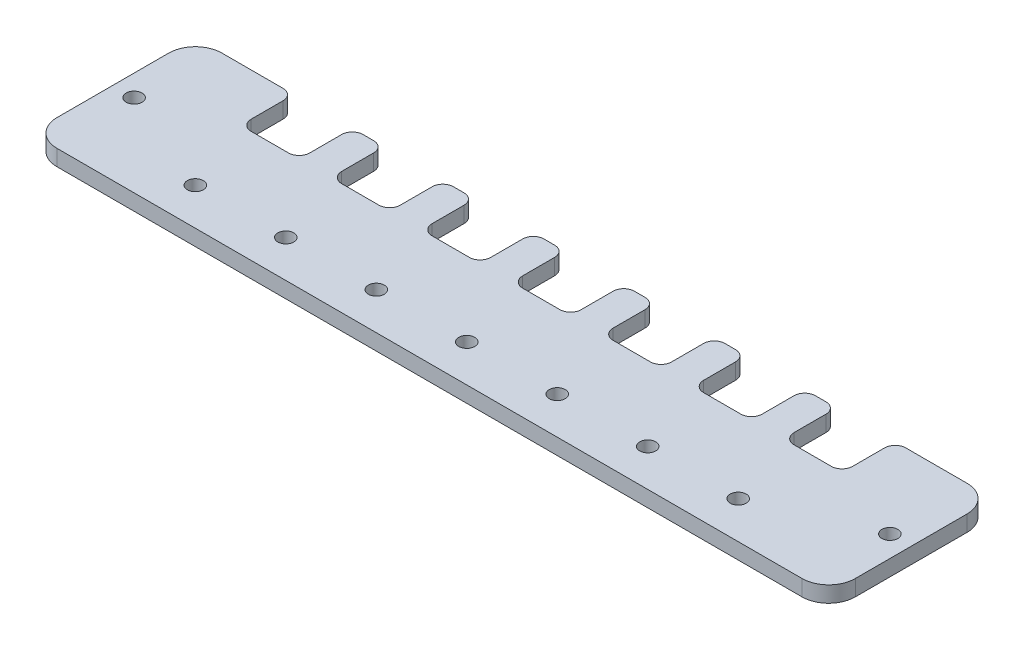
SolidWorks part; units mm, degrees
ref_plane "Front Plane" through (0, 0, 0) normal (0, 0, 1) x (1, 0, 0)
ref_plane "Top Plane" through (0, 0, 0) normal (0, 1, 0) x (1, 0, 0)
ref_plane "Right Plane" through (0, 0, 0) normal (1, 0, 0) x (0, 0, -1)
sketch "Sketch1" plane through (0, 0, 0) normal (0, 1, 0) x (1, 0, 0)
  line L0 (-75, -8.5) -> (75, -8.5) construction
  line L1 (70, 15.5) -> (58.5, 15.5)
  line L2 (75, 10.5) -> (75, -10.5)
  line L3 (70, -15.5) -> (-70, -15.5)
  line L4 (-75, 10.5) -> (-75, -10.5)
  line L5 (75, 15.5) -> (-75, -15.5) construction
  line L6 (75, -15.5) -> (-75, 15.5) construction
  line L7 (-75, 0) -> (75, 0) construction
  line L8 (0, 17.5) -> (0, -15.5) construction
  line L9 (-56.5, 7.5) -> (56.5, 7.5) construction
  line L10 (-54.5, 7.5) -> (-47.5, 7.5) construction
  line L12 (-54.5, 5.5) -> (-47.5, 5.5)
  line L15 (-58.5, 15.5) -> (-70, 15.5)
  line L18 (-51, -8.5) -> (-51, 7.5) construction
  line L21 (-37.5, 5.5) -> (-30.5, 5.5)
  line L24 (-39.5, 7.5) -> (-39.5, 13.5)
  line L27 (-28.5, 7.5) -> (-28.5, 13.5)
  line L30 (-37.5, 7.5) -> (-30.5, 7.5) construction
  line L31 (-20.5, 5.5) -> (-13.5, 5.5)
  line L32 (-56.5, 7.5) -> (-56.5, 13.5)
  line L33 (-45.5, 7.5) -> (-45.5, 13.5)
  line L34 (-22.5, 7.5) -> (-22.5, 13.5)
  line L35 (-11.5, 7.5) -> (-11.5, 13.5)
  line L36 (-20.5, 7.5) -> (-13.5, 7.5) construction
  line L37 (-3.5, 5.5) -> (3.5, 5.5)
  line L38 (-5.5, 7.5) -> (-5.5, 13.5)
  line L39 (5.5, 7.5) -> (5.5, 13.5)
  line L40 (-3.5, 7.5) -> (3.5, 7.5) construction
  line L41 (13.5, 5.5) -> (20.5, 5.5)
  line L42 (11.5, 7.5) -> (11.5, 13.5)
  line L43 (22.5, 7.5) -> (22.5, 13.5)
  line L44 (13.5, 7.5) -> (20.5, 7.5) construction
  line L45 (30.5, 5.5) -> (37.5, 5.5)
  line L46 (28.5, 7.5) -> (28.5, 13.5)
  line L47 (39.5, 7.5) -> (39.5, 13.5)
  line L48 (30.5, 7.5) -> (37.5, 7.5) construction
  line L49 (47.5, 5.5) -> (54.5, 5.5)
  line L50 (45.5, 7.5) -> (45.5, 13.5)
  line L51 (56.5, 7.5) -> (56.5, 13.5)
  line L52 (47.5, 7.5) -> (54.5, 7.5) construction
  line L53 (-41.5, 15.5) -> (-43.5, 15.5)
  line L54 (-24.5, 15.5) -> (-26.5, 15.5)
  line L55 (-7.5, 15.5) -> (-9.5, 15.5)
  line L56 (9.5, 15.5) -> (7.5, 15.5)
  line L57 (26.5, 15.5) -> (24.5, 15.5)
  line L58 (43.5, 15.5) -> (41.5, 15.5)
  circle A1 centre (71, 0) radius 1.5
  arc A2 (-56.5, 7.5) -> (-54.5, 5.5) centre (-54.5, 7.5) ccw
  arc A3 (-47.5, 5.5) -> (-45.5, 7.5) centre (-47.5, 7.5) ccw
  circle A16 centre (-51, -8.5) radius 1.5
  circle A17 centre (-34, -8.5) radius 1.5
  circle A18 centre (-17, -8.5) radius 1.5
  circle A19 centre (0, -8.5) radius 1.5
  circle A20 centre (17, -8.5) radius 1.5
  circle A21 centre (34, -8.5) radius 1.5
  circle A22 centre (51, -8.5) radius 1.5
  arc A23 (70, 15.5) -> (75, 10.5) centre (70, 10.5) cw
  arc A24 (75, -10.5) -> (70, -15.5) centre (70, -10.5) cw
  arc A25 (-70, -15.5) -> (-75, -10.5) centre (-70, -10.5) cw
  arc A26 (-70, 15.5) -> (-75, 10.5) centre (-70, 10.5) ccw
  arc A27 (-45.5, 13.5) -> (-43.5, 15.5) centre (-43.5, 13.5) cw
  arc A28 (-56.5, 13.5) -> (-58.5, 15.5) centre (-58.5, 13.5) ccw
  arc A29 (-39.5, 7.5) -> (-37.5, 5.5) centre (-37.5, 7.5) ccw
  arc A30 (-30.5, 5.5) -> (-28.5, 7.5) centre (-30.5, 7.5) ccw
  arc A31 (-28.5, 13.5) -> (-26.5, 15.5) centre (-26.5, 13.5) cw
  arc A32 (-39.5, 13.5) -> (-41.5, 15.5) centre (-41.5, 13.5) ccw
  arc A33 (-22.5, 7.5) -> (-20.5, 5.5) centre (-20.5, 7.5) ccw
  arc A34 (-13.5, 5.5) -> (-11.5, 7.5) centre (-13.5, 7.5) ccw
  arc A35 (-11.5, 13.5) -> (-9.5, 15.5) centre (-9.5, 13.5) cw
  arc A36 (-22.5, 13.5) -> (-24.5, 15.5) centre (-24.5, 13.5) ccw
  arc A37 (-5.5, 7.5) -> (-3.5, 5.5) centre (-3.5, 7.5) ccw
  arc A38 (3.5, 5.5) -> (5.5, 7.5) centre (3.5, 7.5) ccw
  arc A39 (5.5, 13.5) -> (7.5, 15.5) centre (7.5, 13.5) cw
  arc A40 (-5.5, 13.5) -> (-7.5, 15.5) centre (-7.5, 13.5) ccw
  arc A41 (11.5, 7.5) -> (13.5, 5.5) centre (13.5, 7.5) ccw
  arc A42 (20.5, 5.5) -> (22.5, 7.5) centre (20.5, 7.5) ccw
  arc A43 (22.5, 13.5) -> (24.5, 15.5) centre (24.5, 13.5) cw
  arc A44 (11.5, 13.5) -> (9.5, 15.5) centre (9.5, 13.5) ccw
  arc A45 (28.5, 7.5) -> (30.5, 5.5) centre (30.5, 7.5) ccw
  arc A46 (37.5, 5.5) -> (39.5, 7.5) centre (37.5, 7.5) ccw
  arc A47 (39.5, 13.5) -> (41.5, 15.5) centre (41.5, 13.5) cw
  arc A48 (28.5, 13.5) -> (26.5, 15.5) centre (26.5, 13.5) ccw
  arc A49 (45.5, 7.5) -> (47.5, 5.5) centre (47.5, 7.5) ccw
  arc A50 (54.5, 5.5) -> (56.5, 7.5) centre (54.5, 7.5) ccw
  arc A51 (56.5, 13.5) -> (58.5, 15.5) centre (58.5, 13.5) cw
  arc A52 (45.5, 13.5) -> (43.5, 15.5) centre (43.5, 13.5) ccw
  circle A53 centre (-71, 0) radius 1.5
  point P0 (0, 0)
  point P29 (-56.5, 15.5)
  point P31 (0, 0)
  dimension "D4" = 71
  dimension "D5" = 3
  dimension "D11" = 2
  dimension "D14" = 3
  dimension "D16" = 5
  dimension "D13" = 2
  dimension "D10" = 2
  dimension "D1" = 150
  dimension "D2" = 31
  dimension "D3" = 7
  dimension "D8" = 113
  dimension "D9" = 16
  dimension "D12" = 11
  dimension "D17" = 2
  dimension "D18" = 7
  dimension "D19" = 17
  dimension "D20" = 17
  dimension "D15" = 7
extrude "Boss-Extrude1" add sketch "Sketch1" along normal blind 3
